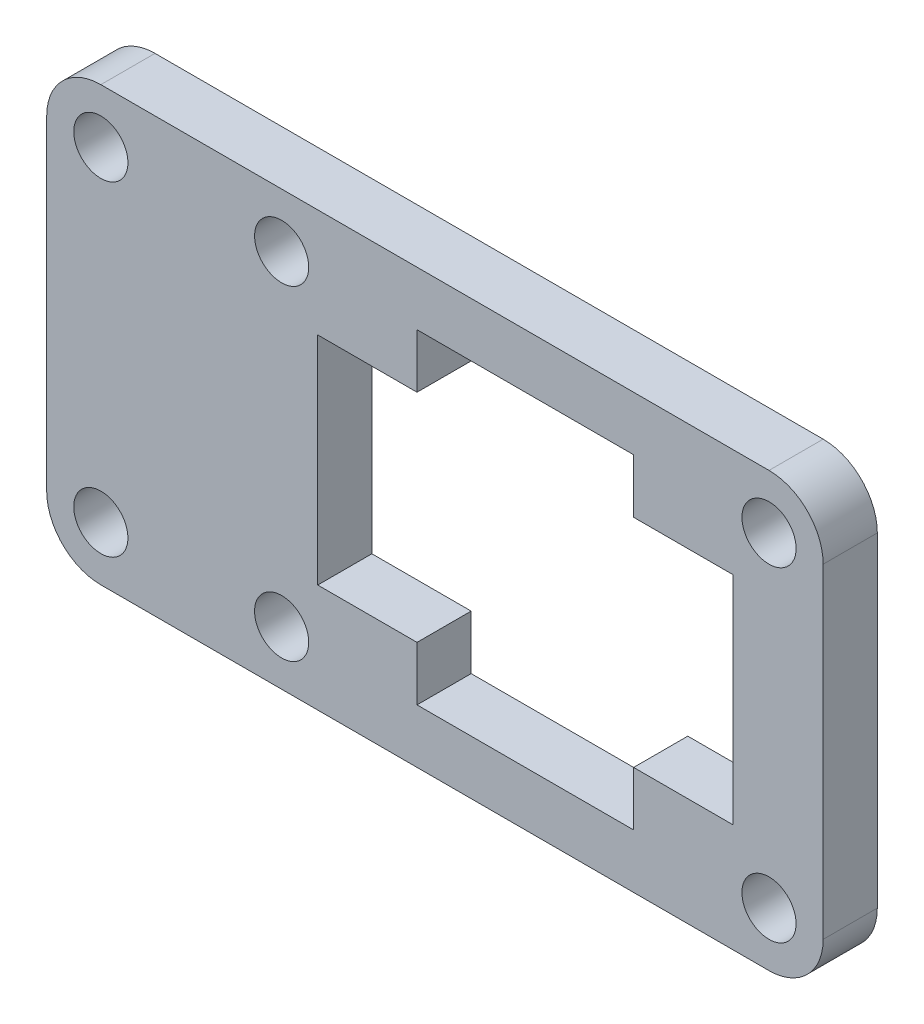
SolidWorks part; units mm, degrees
ref_plane "Plan de face" through (0, 0, 0) normal (0, 0, 1) x (1, 0, 0)
ref_plane "Plan de dessus" through (0, 0, 0) normal (0, 1, 0) x (1, 0, 0)
ref_plane "Plan de droite" through (0, 0, 0) normal (1, 0, 0) x (0, 0, -1)
sketch "Esquisse17" plane through (0, 0, 0) normal (0, 0, 1) x (1, 0, 0)
  line L0 (44.2484, -41.3125) -> (44.2484, -38.3125)
  line L1 (26.7322, -35.3125) -> (63.7484, -35.3125)
  line L2 (23.7322, -38.3125) -> (23.7322, -56.3125)
  line L3 (26.7322, -59.3125) -> (63.7484, -59.3125)
  line L4 (66.7484, -38.3125) -> (66.7484, -56.3125)
  line L5 (38.7484, -53.3125) -> (44.2484, -53.3125)
  line L6 (38.7484, -53.3125) -> (38.7484, -41.3125)
  line L7 (38.7484, -41.3125) -> (44.2484, -41.3125)
  line L8 (61.7484, -53.3125) -> (61.7484, -41.3125)
  line L9 (56.2484, -56.3125) -> (44.2484, -56.3125)
  line L10 (56.2484, -56.3125) -> (56.2484, -53.3125)
  line L11 (56.2484, -38.3125) -> (44.2484, -38.3125)
  line L12 (44.2484, -56.3125) -> (44.2484, -53.3125)
  line L13 (56.2484, -41.3125) -> (61.7484, -41.3125)
  line L14 (56.2484, -41.3125) -> (56.2484, -38.3125)
  line L15 (56.2484, -53.3125) -> (61.7484, -53.3125)
  arc A0 (63.7484, -35.3125) -> (66.7484, -38.3125) centre (63.7484, -38.3125) cw
  arc A1 (63.7484, -59.3125) -> (66.7484, -56.3125) centre (63.7484, -56.3125) ccw
  arc A2 (23.7322, -56.3125) -> (26.7322, -59.3125) centre (26.7322, -56.3125) ccw
  arc A3 (26.7322, -35.3125) -> (23.7322, -38.3125) centre (26.7322, -38.3125) ccw
  circle A4 centre (26.7322, -38.3125) radius 1.5
  circle A5 centre (63.7484, -38.3125) radius 1.5
  circle A6 centre (63.7484, -56.3125) radius 1.5
  circle A7 centre (26.7322, -56.3125) radius 1.5
  circle A8 centre (36.7484, -38.3125) radius 1.5
  circle A9 centre (36.7484, -56.3125) radius 1.5
  dimension "D10" = 3
  dimension "D11" = 3
  dimension "D12" = 3
  dimension "D13" = 3
  dimension "D14" = 3
  dimension "D15" = 3
  dimension "D16" = 3
  dimension "D18" = 27
  dimension "D1" = 12
  dimension "D2" = 3
  dimension "D3" = 3
  dimension "D4" = 3
  dimension "D5" = 3
  dimension "D6" = 5.5
  dimension "D7" = 12
  dimension "D8" = 5.5
  dimension "D9" = 5
  dimension "D17" = 27
extrude "Boss.-Extru.17" add sketch "Esquisse17" along normal blind 3 separate body
